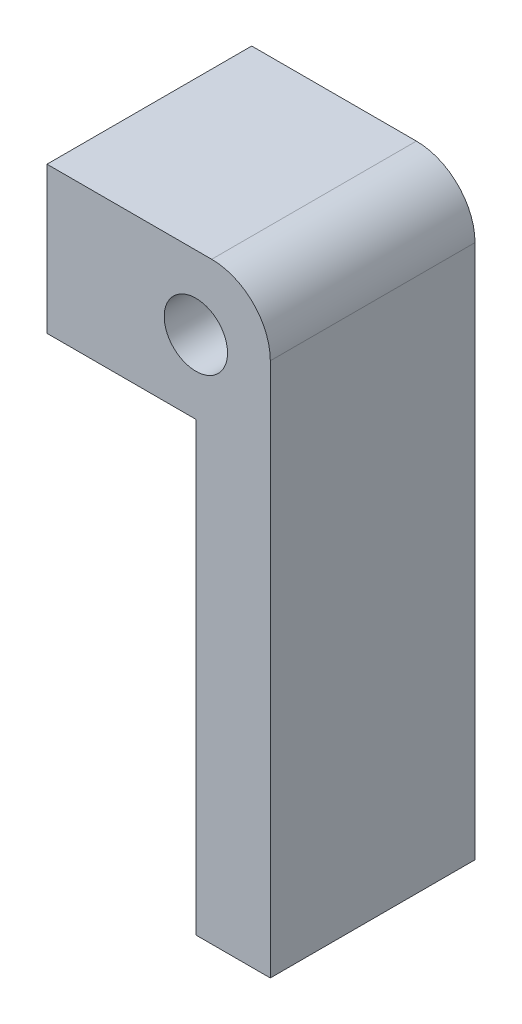
SolidWorks part; units mm, degrees
ref_plane "Front Plane" through (0, 0, 0) normal (0, 0, 1) x (1, 0, 0)
ref_plane "Top Plane" through (0, 0, 0) normal (0, 1, 0) x (1, 0, 0)
ref_plane "Right Plane" through (0, 0, 0) normal (1, 0, 0) x (0, 0, -1)
sketch "Sketch1" plane through (0, 0, 0) normal (0, 0, 1) x (1, 0, 0)
  line L0 (0, 0) -> (25.4, 0)
  line L1 (25.4, 0) -> (25.4, -76.2)
  line L2 (25.4, -76.2) -> (38.1, -76.2)
  line L3 (0, 0) -> (0, 25)
  line L4 (0, 25) -> (38.1, 25)
  line L5 (38.1, 25) -> (38.1, -76.2)
  line L6 (25.4, 0) -> (25.4, 12.5)
  circle A0 centre (25.4, 12.5) radius 5.4
  dimension "D6" = 10.8
  dimension "D1" = 25.4
  dimension "D2" = 76.2
  dimension "D3" = 25
  dimension "D4" = 12.7
  dimension "D5" = 12.5
extrude "Boss-Extrude1" add sketch "Sketch1" along normal blind 34.925
fillet "Fillet1" radius 10 1 edges at (38.1, 25, 17.4625)
